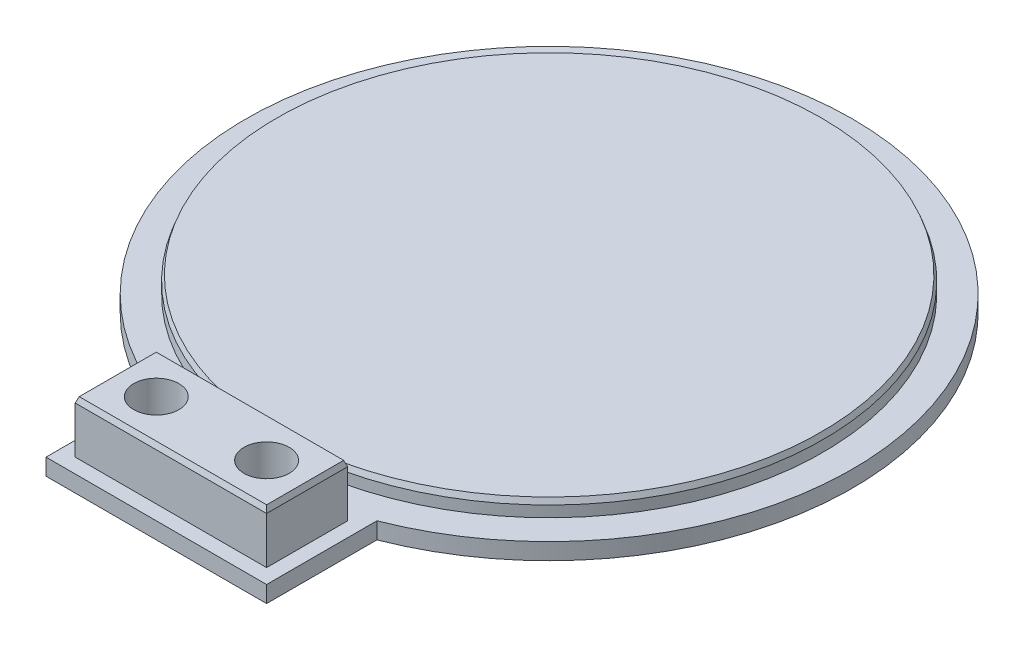
SolidWorks part; units mm, degrees
ref_plane "Спереди" through (0, 0, 0) normal (0, 0, 1) x (1, 0, 0)
ref_plane "Сверху" through (0, 0, 0) normal (0, 1, 0) x (1, 0, 0)
ref_plane "Справа" through (0, 0, 0) normal (1, 0, 0) x (0, 0, -1)
sketch "Sketch1" plane through (0, 0, 0) normal (0, 1, 0) x (1, 0, 0)
  circle A0 centre (0, 0) radius 55
  dimension "D1" = 110
extrude "Boss-Extrude1" add sketch "Sketch1" along normal blind 3
sketch "Sketch9" plane through (0, 0, 0) normal (0, -1, 0) x (1, 0, 0)
  line L0 (0, -55) -> (0, 55) construction
  line L2 (-20, 51.2348) -> (20, 51.2348)
  line L3 (-20, 51.2348) -> (-20, 71.2348)
  line L4 (-20, 71.2348) -> (20, 71.2348)
  line L5 (20, 51.2348) -> (20, 71.2348)
  line L6 (-20, 51.2348) -> (20, 71.2348) construction
  line L7 (-20, 71.2348) -> (20, 51.2348) construction
  circle A0 centre (0, 0) radius 55 construction
  point P5 (0, 61.2348)
  dimension "D1" = 40
  dimension "D2" = 20
extrude "Boss-Extrude4" add sketch "Sketch9" against normal up to surface (3 mm away) up to face at (0, 3, 55)
sketch "Sketch11" plane through (0, 3, 0) normal (0, 1, 0) x (1, 0, 0)
  line L0 (-20, -61.2348) -> (20, -61.2348) construction
  line L1 (-20, -71.2348) -> (-20, -51.2348) construction
  line L2 (20, -51.2348) -> (20, -71.2348) construction
  circle A0 centre (-10, -61.2348) radius 4.1
  circle A1 centre (10, -61.2348) radius 4.1
  point P10 (0, -61.2348)
  dimension "D1" = 8.2
  dimension "D2" = 20
  dimension "D3" = 10
extrude "Cut-Extrude6" cut sketch "Sketch11" against normal through all
sketch "Sketch15" plane through (0, 3, 0) normal (0, 1, 0) x (1, 0, 0)
  circle A0 centre (0, 0) radius 49.7
  arc A1 (20, -51.2348) -> (-20, -51.2348) centre (0, 0) ccw construction
  dimension "D1" = 5.3
extrude "Boss-Extrude6" add sketch "Sketch15" along normal blind 3
chamfer "Chamfer2" distance 1 angle 20 1 edges at (0, 6, 49.7)
sketch "Sketch16" plane through (0, 3, 0) normal (0, 1, 0) x (1, 0, 0)
  line L0 (-10, -61.2348) -> (10, -61.2348) construction
  line L2 (17.35, -68.5848) -> (-17.35, -68.5848)
  line L3 (17.35, -68.5848) -> (17.35, -53.8848)
  line L4 (17.35, -53.8848) -> (-17.35, -53.8848)
  line L5 (-17.35, -68.5848) -> (-17.35, -53.8848)
  line L6 (17.35, -68.5848) -> (-17.35, -53.8848) construction
  line L7 (17.35, -53.8848) -> (-17.35, -68.5848) construction
  circle A0 centre (-10, -61.2348) radius 4.1
  circle A1 centre (10, -61.2348) radius 4.1
  point P4 (0, -61.2348)
  dimension "D1" = 14.7
  dimension "D2" = 34.7
extrude "Boss-Extrude7" add sketch "Sketch16" along normal blind 9.5
chamfer "Chamfer3" distance 1 angle 20 4 edges at (0, 12.5, 68.5848) (17.35, 12.5, 61.2348) (0, 12.5, 53.8848) (-17.35, 12.5, 61.2348)
